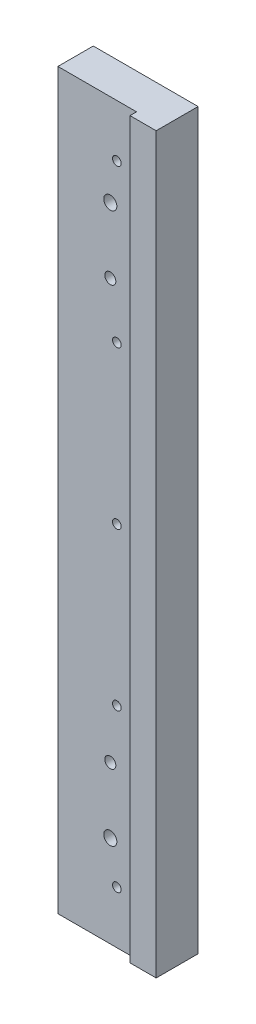
SolidWorks part; units mm, degrees
material "1023 Листовая углеродистая сталь (SS)"
ref_plane "Front" through (0, 0, 0) normal (0, 0, 1) x (1, 0, 0)
ref_plane "Top" through (0, 0, 0) normal (0, 1, 0) x (1, 0, 0)
ref_plane "Right" through (0, 0, 0) normal (1, 0, 0) x (0, 0, -1)
sketch "Sketch1" plane through (0, 0, 0) normal (0, 0, 1) x (1, 0, 0)
  line L1 (-20, 140) -> (20, 140)
  line L2 (-20, 140) -> (-20, -140)
  line L3 (-20, -140) -> (20, -140)
  line L4 (20, 140) -> (20, -140)
  line L5 (-20, 140) -> (20, -140) construction
  line L6 (-20, -140) -> (20, 140) construction
  point P0 (0, 0)
  dimension "D1" = 280
  dimension "D2" = 40
extrude "Extrude1" add sketch "Sketch1" along normal blind 16
sketch "Sketch2" plane through (0, -140, 0) normal (0, -1, 0) x (1, 0, 0)
  line L1 (-20, 16) -> (10, 16)
  line L2 (-20, 16) -> (-20, 13.5)
  line L3 (-20, 13.5) -> (10, 13.5)
  line L4 (10, 16) -> (10, 13.5)
  dimension "D1" = 2.5
  dimension "D2" = 30
extrude "Extrude2" cut sketch "Sketch2" against normal up to next
hole_wizard "M4 Tapped Hole1" positions "Sketch3" profile "Sketch4" tap size "M4" standard "DIN" end condition through all
sketch "Sketch3" plane through (0, 0, 13.5) normal (0, 0, 1) x (1, 0, 0)
  line L0 (10, 140) -> (10, -140) construction
  line L1 (-20, -140) -> (10, -140) construction
  point P0 (2.5, -120)
  point P12 (2.5, -60)
  point P13 (2.5, 0)
  point P14 (2.5, 60)
  point P15 (2.5, 120)
  dimension "D1" = 7.5
  dimension "D2" = 20
  dimension "D3" = 5
sketch "Sketch4" plane through (2.5, -120, 13.5) normal (1, 0, 0) x (0, -1, 0)
  line L0 (0, 0) -> (0, 13.5)
  line L1 (0, 13.5) -> (1.65, 13.5)
  line L2 (1.65, 13.5) -> (1.65, 0)
  line L5 (1.65, 0) -> (0, 0)
  line L11 (0, -6.35) -> (0, 107.95) construction
  dimension "Диаметр проходного сверла" = 3.3
  dimension "Глубина проходного сверла" = 13.5
cosmetic thread "Cosmetic Thread1" parameters "D2"=4
cosmetic thread "Cosmetic Thread2" parameters "D2"=4
cosmetic thread "Cosmetic Thread3" parameters "D2"=4
cosmetic thread "Cosmetic Thread4" parameters "D2"=4
cosmetic thread "Cosmetic Thread5" parameters "D2"=4
hole_wizard "M6 Tapped Hole1" positions "Sketch5" profile "Sketch6" tap size "M6" standard "DIN" end condition through all
sketch "Sketch5" plane through (0, 0, 0) normal (0, 0, -1) x (-1, 0, 0)
  point P0 (0, 105)
  point P3 (0, -105)
sketch "Sketch6" plane through (0, 105, 0) normal (1, 0, 0) x (0, 1, 0)
  line L0 (0, 0) -> (0, 16)
  line L1 (0, 16) -> (2.5, 16)
  line L2 (2.5, 16) -> (2.5, 0)
  line L5 (2.5, 0) -> (0, 0)
  line L11 (0, -6.35) -> (0, 107.95) construction
  dimension "Диаметр проходного сверла" = 5
  dimension "Глубина проходного сверла" = 16
cosmetic thread "Cosmetic Thread6" parameters "D2"=6
cosmetic thread "Cosmetic Thread7" parameters "D2"=6
hole_wizard "M5 Tapped Hole1" positions "Sketch7" profile "Sketch8" tap size "M5" standard "DIN" end condition up to next
sketch "Sketch7" plane through (0, 0, 13.5) normal (0, 0, 1) x (1, 0, 0)
  point P0 (0, 80)
  point P3 (0, -80)
sketch "Sketch8" plane through (0, 80, 13.5) normal (1, 0, 0) x (0, -1, 0)
  line L0 (0, 0) -> (0, 13.5)
  line L1 (0, 13.5) -> (2.1, 13.5)
  line L2 (2.1, 13.5) -> (2.1, 0)
  line L5 (2.1, 0) -> (0, 0)
  line L11 (0, -6.35) -> (0, 107.95) construction
  dimension "Диаметр проходного сверла" = 4.2
  dimension "Глубина проходного сверла" = 13.5
cosmetic thread "Cosmetic Thread8" parameters "D2"=5
cosmetic thread "Cosmetic Thread9" parameters "D2"=5
